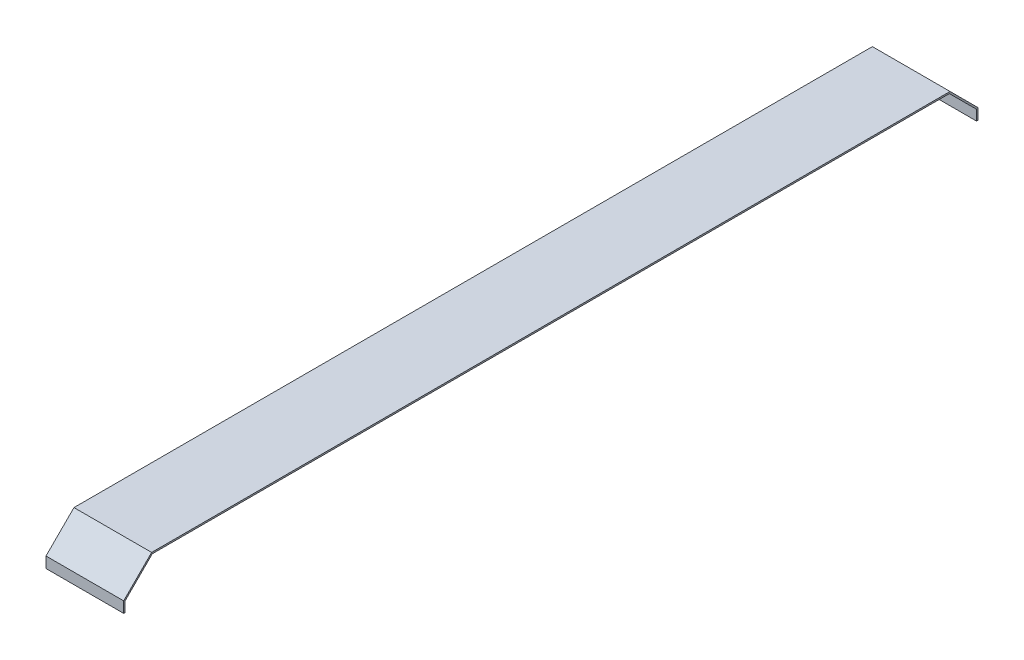
SolidWorks part; units mm, degrees
ref_plane "前视基准面" through (0, 0, 0) normal (0, 0, 1) x (1, 0, 0)
ref_plane "上视基准面" through (0, 0, 0) normal (0, 1, 0) x (1, 0, 0)
ref_plane "右视基准面" through (0, 0, 0) normal (1, 0, 0) x (0, 0, -1)
sketch "草图1" plane through (0, 0, 0) normal (1, 0, 0) x (0, 0, -1)
  line L0 (-257, 0) -> (257, 0)
  line L1 (275, -18) -> (275, -25)
  line L2 (-275, -18) -> (-275, -25)
  line L3 (257, 0) -> (275, -18)
  line L4 (-275, -18) -> (-257, 0)
  line L5 (-274, -18.4142) -> (-274, -25)
  line L6 (274, -25) -> (275, -25)
  line L7 (-275, -25) -> (-274, -25)
  line L8 (274, -18.4142) -> (274, -25)
  line L9 (-274, -18.4142) -> (-256.5858, -1)
  line L10 (-256.5858, -1) -> (256.5858, -1)
  line L11 (256.5858, -1) -> (274, -18.4142)
  line L14 (-274, -18.4142) -> (-274, -24) construction
  line L15 (-274, -24) -> (-274, -24) construction
  line L16 (274, -18.4142) -> (274, -24) construction
  line L17 (274, -24) -> (274, -24) construction
  point P0 (-275, 0)
  point P1 (275, 0)
  dimension "D1" = 25
  dimension "D2" = 25
  dimension "D3" = 550
  dimension "D4" = 275
  dimension "D5" = 1
extrude "凸台-拉伸1" add sketch "草图1" along normal blind 50
